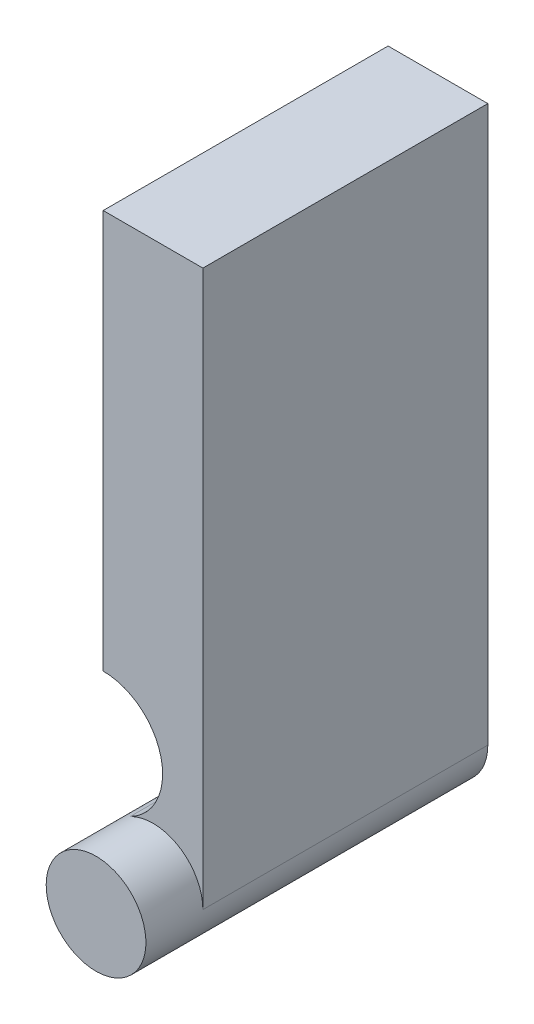
SolidWorks part; units mm, degrees
ref_plane "Front Plane" through (0, 0, 0) normal (0, 0, 1) x (1, 0, 0)
ref_plane "Top Plane" through (0, 0, 0) normal (0, 1, 0) x (1, 0, 0)
ref_plane "Right Plane" through (0, 0, 0) normal (1, 0, 0) x (0, 0, -1)
sketch "Szkic1" plane through (0, 0, 0) normal (0, 0, 1) x (1, 0, 0)
  line L0 (1.75, 0) -> (1.75, 19.5)
  line L1 (-1.75, 19.5) -> (-1.75, 5.5)
  line L2 (-1.75, 19.5) -> (1.75, 19.5)
  arc A0 (-0.7983, 1.5573) -> (1.75, 0) centre (0, 0) ccw
  arc A1 (-1.75, 5.5) -> (-0.7983, 1.5573) centre (-1.75, 3.4138) cw
  dimension "D1" = 3.5
  dimension "D2" = 14
  dimension "D3" = 3.5
  dimension "D4" = 19.5
extrude "Dodanie-wyciągnięcie1" add sketch "Szkic1" along normal blind 10
sketch "Szkic2" plane through (0, 0, 0) normal (0, 0, -1) x (-1, 0, 0)
  circle A0 centre (0, 0) radius 1.75
  arc A1 (-1.75, 0) -> (0.7983, 1.5573) centre (0, 0) ccw construction
extrude "Dodanie-wyciągnięcie2" add sketch "Szkic2" against normal blind 12
